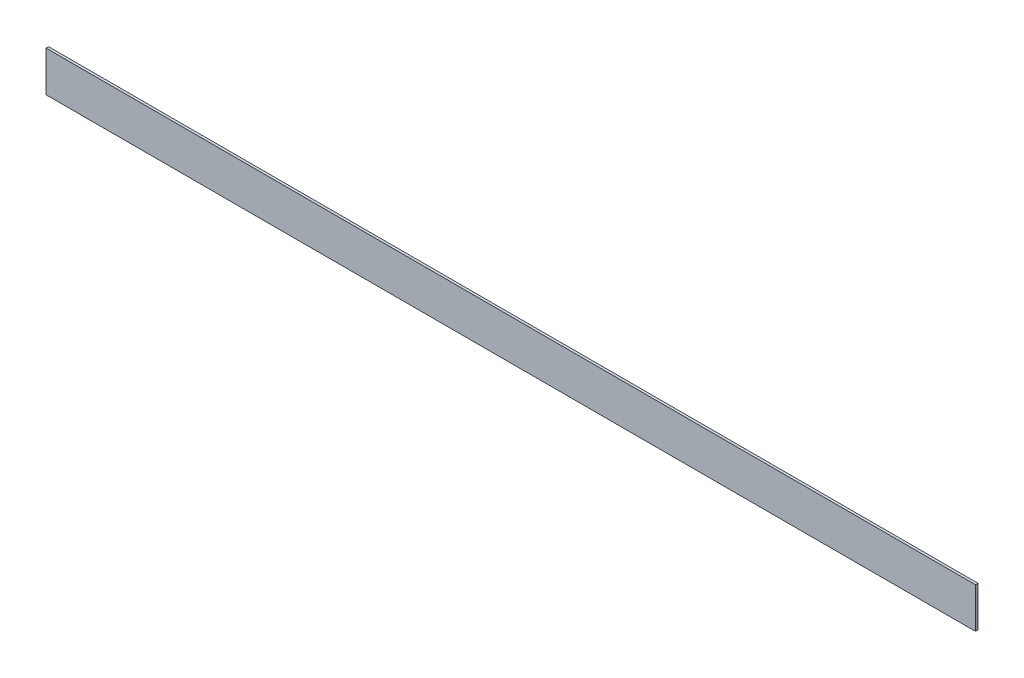
SolidWorks part; units mm, degrees
ref_plane "Front Plane" through (0, 0, 0) normal (0, 0, 1) x (1, 0, 0)
ref_plane "Top Plane" through (0, 0, 0) normal (0, 1, 0) x (1, 0, 0)
ref_plane "Right Plane" through (0, 0, 0) normal (1, 0, 0) x (0, 0, -1)
sketch "Sketch1" plane through (0, 0, 0) normal (0, 0, 1) x (1, 0, 0)
  line L1 (-292.1, 12.7) -> (292.1, 12.7)
  line L2 (-292.1, 12.7) -> (-292.1, -12.7)
  line L3 (-292.1, -12.7) -> (292.1, -12.7)
  line L4 (292.1, 12.7) -> (292.1, -12.7)
  line L5 (-292.1, 12.7) -> (292.1, -12.7) construction
  line L6 (-292.1, -12.7) -> (292.1, 12.7) construction
  point P0 (0, 0)
  dimension "D1" = 25.4
  dimension "D2" = 584.2
extrude "Boss-Extrude1" add sketch "Sketch1" along normal blind 1.5875
